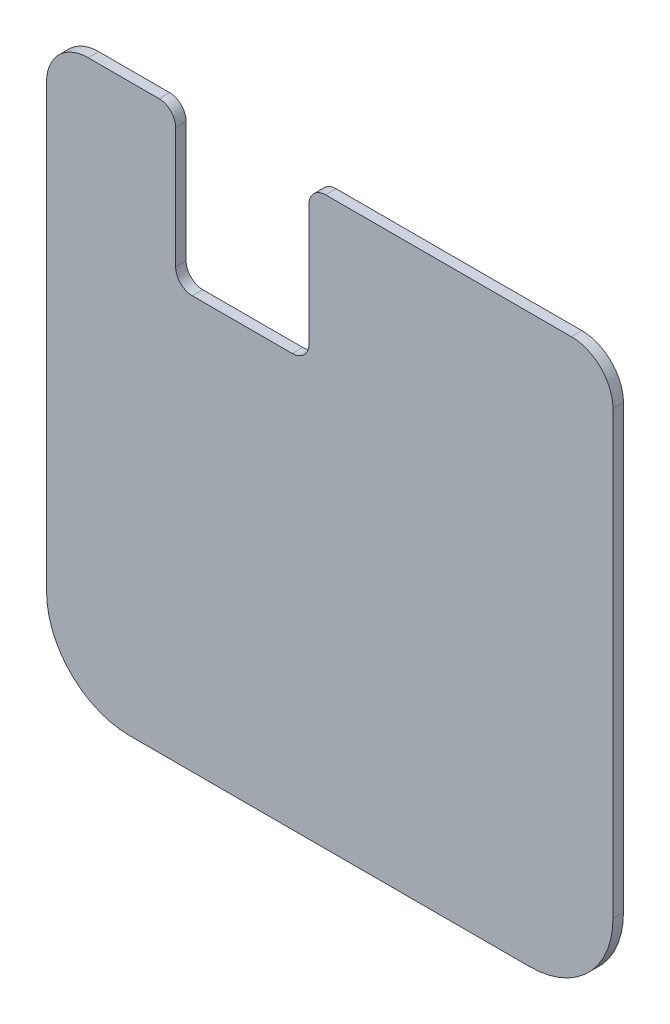
SolidWorks part; units mm, degrees
ref_plane "Front Plane" through (0, 0, 0) normal (0, 0, 1) x (1, 0, 0)
ref_plane "Top Plane" through (0, 0, 0) normal (0, 1, 0) x (1, 0, 0)
ref_plane "Right Plane" through (0, 0, 0) normal (1, 0, 0) x (0, 0, -1)
sketch "Sketch1" plane through (0, 0, 0) normal (0, 0, 1) x (1, 0, 0)
  line L0 (37.7952, -26.0147) -> (37.7952, -93.3247)
  line L1 (50.4952, -106.0247) -> (111.4552, -106.0247)
  line L2 (124.1552, -93.3247) -> (124.1552, -26.0147)
  line L3 (117.8052, -19.6647) -> (80.3402, -19.6647)
  line L4 (77.8002, -22.2047) -> (77.8002, -40.6197)
  line L5 (75.2602, -43.1597) -> (60.0202, -43.1597)
  line L6 (57.4802, -40.6197) -> (57.4802, -22.2047)
  line L7 (54.9402, -19.6647) -> (44.1452, -19.6647)
  arc A0 (44.1452, -19.6647) -> (37.7952, -26.0147) centre (44.1452, -26.0147) ccw
  arc A1 (37.7952, -93.3247) -> (50.4952, -106.0247) centre (50.4952, -93.3247) ccw
  arc A2 (111.4552, -106.0247) -> (124.1552, -93.3247) centre (111.4552, -93.3247) ccw
  arc A3 (124.1552, -26.0147) -> (117.8052, -19.6647) centre (117.8052, -26.0147) ccw
  arc A4 (80.3402, -19.6647) -> (77.8002, -22.2047) centre (80.3402, -22.2047) ccw
  arc A5 (77.8002, -40.6197) -> (75.2602, -43.1597) centre (75.2602, -40.6197) cw
  arc A6 (60.0202, -43.1597) -> (57.4802, -40.6197) centre (60.0202, -40.6197) cw
  arc A7 (57.4802, -22.2047) -> (54.9402, -19.6647) centre (54.9402, -22.2047) ccw
extrude "BOARD" add sketch "Sketch1" along normal blind 1.6002 separate body
ref_plane "Plane1" through (0, 0, 1.6002) normal (0, 0, 1) x (1, 0, 0)
